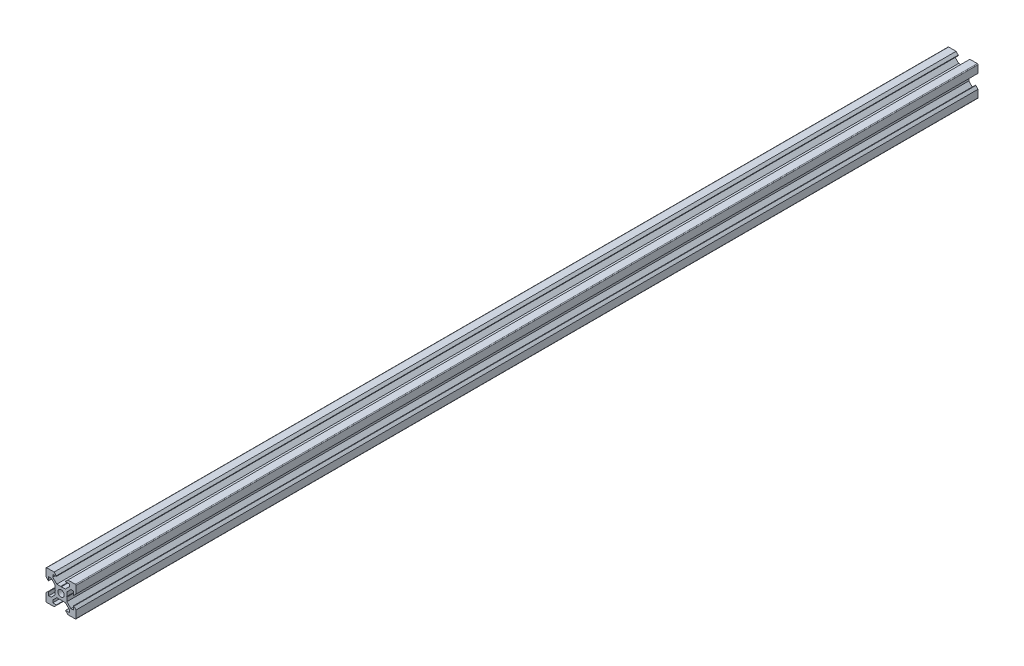
SolidWorks part; units mm, degrees
material "6061-T6 (SS)"
ref_plane "Front Plane" through (0, 0, 0) normal (0, 0, 1) x (1, 0, 0)
ref_plane "Top Plane" through (0, 0, 0) normal (0, 1, 0) x (1, 0, 0)
ref_plane "Right Plane" through (0, 0, 0) normal (1, 0, 0) x (0, 0, -1)
sketch "Sketch1" plane through (0, 0, 0) normal (0, 0, 1) x (1, 0, 0)
  line L1 (9.5, -10) -> (-9.5, -10)
  line L2 (10, -9.5) -> (10, 9.5)
  line L3 (9.5, 10) -> (-9.5, 10)
  line L4 (-10, -9.5) -> (-10, 9.5)
  line L5 (10, -10) -> (-10, 10) construction
  line L6 (10, 10) -> (-10, -10) construction
  circle A0 centre (0, 0) radius 2.1
  arc A1 (-9.5, 10) -> (-10, 9.5) centre (-9.5, 9.5) ccw
  arc A2 (10, 9.5) -> (9.5, 10) centre (9.5, 9.5) ccw
  arc A3 (9.5, -10) -> (10, -9.5) centre (9.5, -9.5) ccw
  arc A4 (-9.5, -10) -> (-10, -9.5) centre (-9.5, -9.5) cw
  point P0 (0, 0)
  line B0 (0, 0) -> (0, 10) construction
  line B1 (0, 3.69) -> (-0.21, 3.9)
  line B2 (-0.21, 3.9) -> (-2.8393, 3.9)
  line B3 (-2.8393, 3.9) -> (-5.5, 6.5607)
  line B4 (-5.5, 6.5607) -> (-5.5, 8.2)
  line B5 (-5.5, 8.2) -> (-3.125, 8.2)
  line B6 (-3.125, 8.2) -> (-3.125, 8.545)
  line B7 (-3.125, 8.545) -> (-4.58, 10)
  line B8 (-4.58, 10) -> (4.58, 10)
  line B9 (0, 0) -> (-5.9132, 5.9132) construction
  line B10 (3.125, 8.545) -> (4.58, 10)
  line B11 (3.125, 8.2) -> (3.125, 8.545)
  line B12 (5.5, 8.2) -> (3.125, 8.2)
  line B13 (5.5, 6.5607) -> (5.5, 8.2)
  line B14 (2.8393, 3.9) -> (5.5, 6.5607)
  line B15 (0.21, 3.9) -> (2.8393, 3.9)
  line B16 (0, 3.69) -> (0.21, 3.9)
  line B17 (0, 0) -> (-10, 0) construction
  line B18 (-3.69, 0) -> (-3.9, -0.21)
  line B19 (-3.9, -0.21) -> (-3.9, -2.8393)
  line B20 (-3.9, -2.8393) -> (-6.5607, -5.5)
  line B21 (-6.5607, -5.5) -> (-8.2, -5.5)
  line B22 (-8.2, -5.5) -> (-8.2, -3.125)
  line B23 (-8.2, -3.125) -> (-8.545, -3.125)
  line B24 (-8.545, -3.125) -> (-10, -4.58)
  line B25 (-10, -4.58) -> (-10, 4.58)
  line B26 (0, 0) -> (-5.9132, -5.9132) construction
  line B27 (-8.545, 3.125) -> (-10, 4.58)
  line B28 (-8.2, 3.125) -> (-8.545, 3.125)
  line B29 (-8.2, 5.5) -> (-8.2, 3.125)
  line B30 (-6.5607, 5.5) -> (-8.2, 5.5)
  line B31 (-3.9, 2.8393) -> (-6.5607, 5.5)
  line B32 (-3.9, 0.21) -> (-3.9, 2.8393)
  line B33 (-3.69, 0) -> (-3.9, 0.21)
  line B34 (0, 0) -> (0, -10) construction
  line B35 (0, -3.69) -> (0.21, -3.9)
  line B36 (0.21, -3.9) -> (2.8393, -3.9)
  line B37 (2.8393, -3.9) -> (5.5, -6.5607)
  line B38 (5.5, -6.5607) -> (5.5, -8.2)
  line B39 (5.5, -8.2) -> (3.125, -8.2)
  line B40 (3.125, -8.2) -> (3.125, -8.545)
  line B41 (3.125, -8.545) -> (4.58, -10)
  line B42 (4.58, -10) -> (-4.58, -10)
  line B43 (0, 0) -> (5.9132, -5.9132) construction
  line B44 (-3.125, -8.545) -> (-4.58, -10)
  line B45 (-3.125, -8.2) -> (-3.125, -8.545)
  line B46 (-5.5, -8.2) -> (-3.125, -8.2)
  line B47 (-5.5, -6.5607) -> (-5.5, -8.2)
  line B48 (-2.8393, -3.9) -> (-5.5, -6.5607)
  line B49 (-0.21, -3.9) -> (-2.8393, -3.9)
  line B50 (0, -3.69) -> (-0.21, -3.9)
  line B51 (0, 0) -> (10, 0) construction
  line B52 (3.69, 0) -> (3.9, 0.21)
  line B53 (3.9, 0.21) -> (3.9, 2.8393)
  line B54 (3.9, 2.8393) -> (6.5607, 5.5)
  line B55 (6.5607, 5.5) -> (8.2, 5.5)
  line B56 (8.2, 5.5) -> (8.2, 3.125)
  line B57 (8.2, 3.125) -> (8.545, 3.125)
  line B58 (8.545, 3.125) -> (10, 4.58)
  line B59 (10, 4.58) -> (10, -4.58)
  line B60 (0, 0) -> (5.9132, 5.9132) construction
  line B61 (8.545, -3.125) -> (10, -4.58)
  line B62 (8.2, -3.125) -> (8.545, -3.125)
  line B63 (8.2, -5.5) -> (8.2, -3.125)
  line B64 (6.5607, -5.5) -> (8.2, -5.5)
  line B65 (3.9, -2.8393) -> (6.5607, -5.5)
  line B66 (3.9, -0.21) -> (3.9, -2.8393)
  line B67 (3.69, 0) -> (3.9, -0.21)
  dimension "D1" = 4.2
  dimension "D3" = 0.5
  dimension "D2" = 20
sketch_block_instance "V Slot 1-4"
sketch_block "V Slot 1" parameters "D1"=10, "D2"=11, "D3"=4.3, "D4"=1.8, "D5"=0.21, "D6"=45, "D7"=9.16, "D8"=1.5, "D9"=6.25
sketch_block_instance "V Slot 1-5"
sketch_block_instance "V Slot 1-6"
sketch_block_instance "V Slot 1-7"
extrude "Boss-Extrude1" add sketch "Sketch1" along normal blind 600 contours B67 B52 B53 B54 B55 B56 B57 B58 L2 A2 L3 B10 B11 B12 B13 B14 B15 B16 B1 B2 B3 B4 B5 B6 B7 A1 L4 B27 B28 B29 B30 B31 B32 B33 B18 B19 B20 B21 B22 B23 B24 A4 L1 B44 B45 B46 B47 B48 B49
